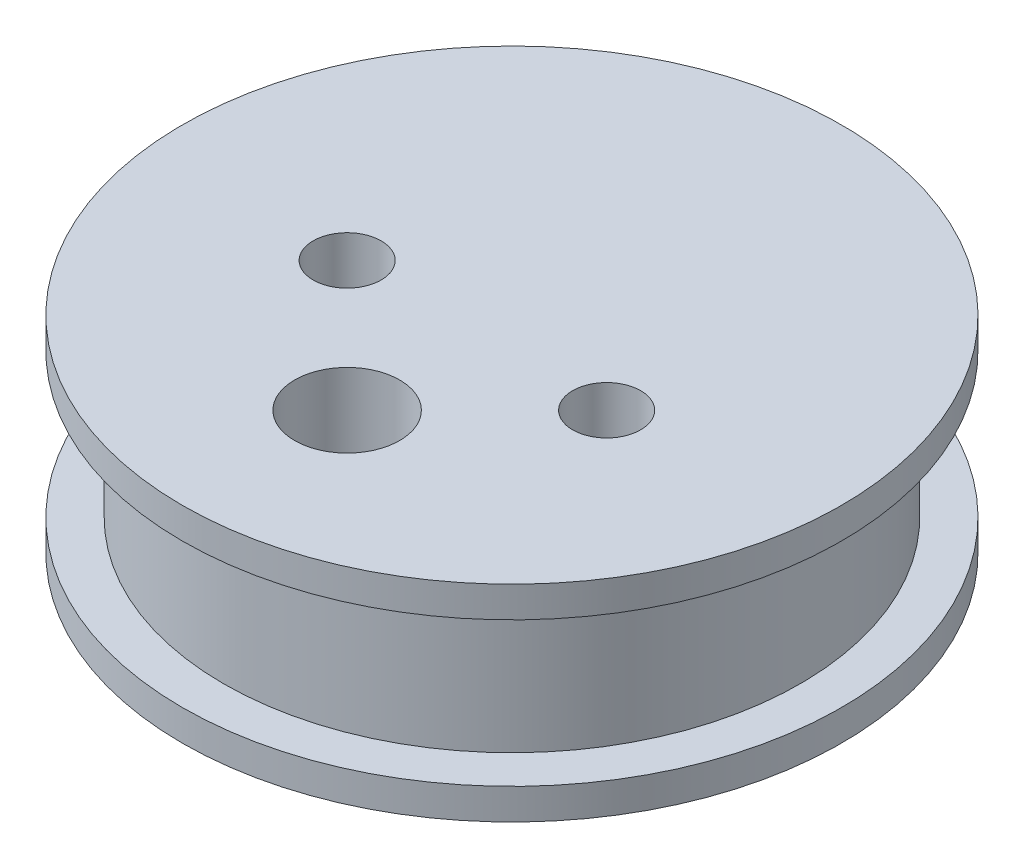
SolidWorks part; units mm, degrees
ref_plane "Front Plane" through (0, 0, 0) normal (0, 0, 1) x (1, 0, 0)
ref_plane "Top Plane" through (0, 0, 0) normal (0, 1, 0) x (1, 0, 0)
ref_plane "Right Plane" through (0, 0, 0) normal (1, 0, 0) x (0, 0, -1)
sketch "Sketch3" plane through (0, 0, 0) normal (0, 0, 1) x (1, 0, 0)
  line L0 (30.48, -1.3614) -> (50.8, -1.3614)
  line L1 (50.8, -1.3614) -> (50.8, 0.5436)
  line L2 (50.8, 0.5436) -> (48.26, 0.5436)
  line L3 (48.26, 0.5436) -> (48.26, 9.4336)
  line L4 (48.26, 9.4336) -> (50.8, 9.4336)
  line L5 (50.8, 9.4336) -> (50.8, 11.3386)
  line L6 (50.8, 11.3386) -> (30.48, 11.3386)
  line L7 (30.48, 11.3386) -> (30.48, -1.3614)
  dimension "D1" = 20.32
  dimension "D2" = 20.32
  dimension "D3" = 8.89
  dimension "D4" = 12.7
  dimension "D5" = 2.54
  dimension "D6" = 1.905
revolve "Revolve1" add sketch "Sketch3" angle 360 about L7
sketch "Sketch4" plane through (0, 11.3386, 0) normal (0, 1, 0) x (1, 0, 0)
  line L0 (30.48, -1.3284) -> (30.48, -20.32) construction
  line L1 (30.48, -20.32) -> (30.48, 20.32) construction
  line L2 (30.48, 20.32) -> (30.48, 0) construction
  line L3 (30.48, 0) -> (50.8, 0) construction
  line L4 (50.8, 0) -> (10.16, 0) construction
  circle A0 centre (30.48, -10.16) radius 3.2385
  circle A1 centre (30.48, 0) radius 20.32 construction
  circle A2 centre (22.48, -2.16) radius 2.0955
  circle A3 centre (38.48, -2.16) radius 2.0955
  dimension "D3" = 6.477
  dimension "D8" = 4.191
  dimension "D9" = 4.191
  dimension "D1" = 0
  dimension "D2" = 10.16
  dimension "D4" = 8
  dimension "D5" = 8
  dimension "D6" = 8
  dimension "D7" = 8
extrude "Cut-Extrude1" cut sketch "Sketch4" against normal through all
